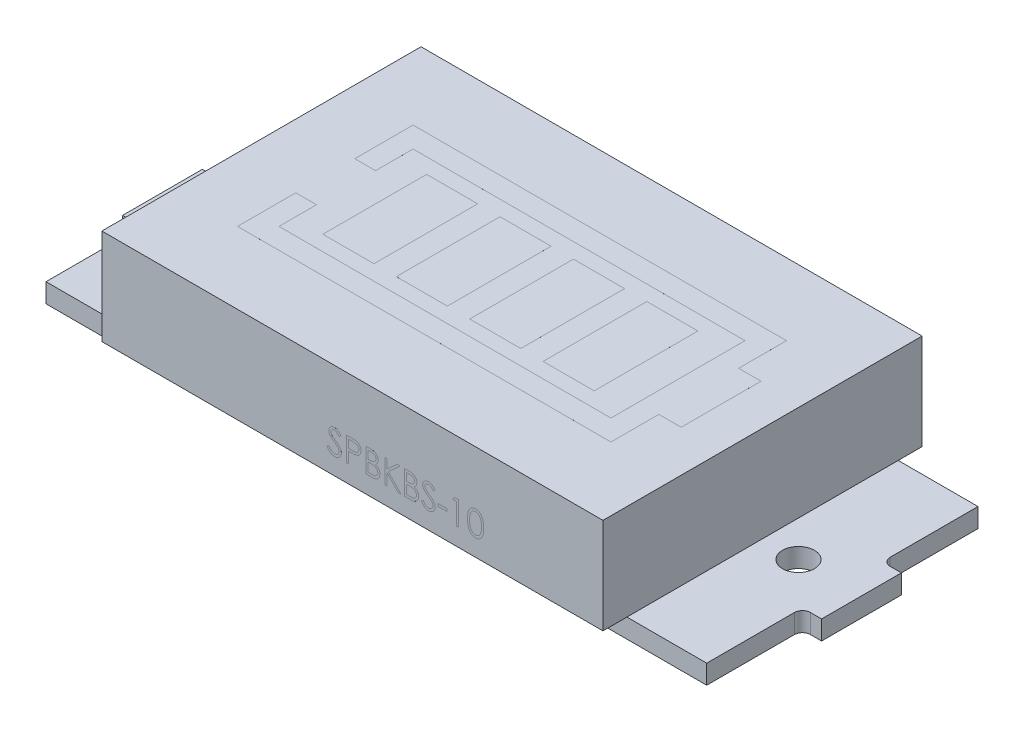
SolidWorks part; units mm, degrees
ref_plane "Plano frontal" through (0, 0, 0) normal (0, 0, 1) x (1, 0, 0)
ref_plane "Plano superior" through (0, 0, 0) normal (0, 1, 0) x (1, 0, 0)
ref_plane "Plano direito" through (0, 0, 0) normal (1, 0, 0) x (0, 0, -1)
sketch "Sketch1" plane through (0, 0, 0) normal (0, 1, 0) x (1, 0, 0)
  line L1 (20.7, -8.5) -> (-20.7, -8.5)
  line L2 (20.7, -8.5) -> (20.7, 8.5)
  line L3 (20.7, 8.5) -> (-20.7, 8.5)
  line L4 (-20.7, -8.5) -> (-20.7, 8.5)
  line L5 (0, 8.5) -> (0, -8.5) construction
  line L6 (20.7, 0) -> (-20.7, 0) construction
  point P0 (0, 0)
  dimension "D1" = 41.4
  dimension "D2" = 17
extrude "Boss-Extrude1" add sketch "Sketch1" along normal mid plane 1.2
sketch "Sketch2" plane through (0, 0, 0) normal (0, 1, 0) x (1, 0, 0)
  line L0 (-20.7, 8.5) -> (-20.7, -8.5) construction
  line L1 (-21.9, 2.5) -> (-20.7, 2.5)
  line L2 (-21.9, 2.5) -> (-21.9, -2.5)
  line L3 (-21.9, -2.5) -> (-20.7, -2.5)
  line L4 (-20.7, 2.5) -> (-20.7, -2.5)
  line L5 (0, -3.9602) -> (0, 3.9602) construction
  line L6 (20.7, 2.5) -> (20.7, -2.5)
  line L7 (21.9, -2.5) -> (20.7, -2.5)
  line L8 (21.9, 2.5) -> (21.9, -2.5)
  line L9 (21.9, 2.5) -> (20.7, 2.5)
  point P6 (-21.9, 0)
  dimension "D1" = 5
  dimension "D2" = 1.2
extrude "Boss-Extrude2" add sketch "Sketch2" along normal mid plane 1.2
fillet "Fillet1" radius 0.5 4 edges at (20.7, 0, -2.5) (20.7, 0, 2.5) (-20.7, 0, 2.5) (-20.7, 0, -2.5)
sketch "Sketch3" plane through (0, 0, 0) normal (0, 1, 0) x (1, 0, 0)
  line L0 (0, -3.9602) -> (0, 3.9602) construction
  circle A0 centre (-17.95, 0) radius 1
  circle A1 centre (17.95, 0) radius 1
  dimension "D1" = 2
  dimension "D2" = 37.9
extrude "Cut-Extrude1" cut sketch "Sketch3" against normal through all both and the other way through all
sketch "Sketch6" plane through (0, -0.6, 0) normal (0, -1, 0) x (1, 0, 0)
  text T0 "<b>MH-DL18S</b>\r\n" font "Century Gothic" height 1
  text T1 "<b>MH-ET-LIVE</b>" font "Century Gothic" height 0.75
extrude "Boss-Extrude5" add sketch "Sketch6" along normal blind 0.0001
sketch "Sketch10" plane through (0, 0, 0) normal (0, 1, 0) x (1, 0, 0)
  line L1 (20.7, 8.5) -> (-20.7, 8.5) construction
  line L3 (-20.7, 8.5) -> (-20.7, 3) construction
  circle A0 centre (-19.2, 7) radius 0.5
  circle A1 centre (-19.2, 4.4) radius 0.5
  dimension "D1" = 1
  dimension "D2" = 1
  dimension "D3" = 1.6
  dimension "D4" = 1
extrude "Cut-Extrude2" cut sketch "Sketch10" against normal through all both and the other way through all
sketch "Sketch11" plane through (0, 0.6, 0) normal (0, 1, 0) x (1, 0, 0)
  line L0 (-19.25, 7) -> (-19.15, 7) construction
  line L1 (-19.25, 7.6) -> (-19.15, 7.6)
  line L2 (-19.25, 6.4) -> (-19.15, 6.4)
  line L3 (-19.25, 4.4) -> (-19.15, 4.4) construction
  line L4 (-19.25, 5) -> (-19.15, 5)
  line L5 (-19.25, 3.8) -> (-19.15, 3.8)
  arc A0 (-19.25, 7.6) -> (-19.25, 6.4) centre (-19.25, 7) ccw
  arc A1 (-19.15, 6.4) -> (-19.15, 7.6) centre (-19.15, 7) ccw
  circle A2 centre (-19.2, 7) radius 0.5 construction
  circle A3 centre (-19.2, 7) radius 0.5
  circle A4 centre (-19.2, 4.4) radius 0.5 construction
  circle A5 centre (-19.2, 4.4) radius 0.5
  arc A6 (-19.25, 5) -> (-19.25, 3.8) centre (-19.25, 4.4) ccw
  arc A7 (-19.15, 3.8) -> (-19.15, 5) centre (-19.15, 4.4) ccw
  point P2 (-19.2, 7)
  point P16 (-19.2, 4.4)
  dimension "D2" = 0.1
  dimension "D1" = 0.05
extrude "Boss-Extrude9" add sketch "Sketch11" along normal blind 0.0001
mirror "Mirror1" about plane through (0, 0, 0) normal (0, 1, 0) of "Boss-Extrude9"
sketch "Sketch12" plane through (0, 0.6, 0) normal (0, 1, 0) x (1, 0, 0)
  line L0 (-20.7, -8.5) -> (20.7, -8.5) construction
  line L1 (-17.6069, 7.1399) -> (-16.6453, 7.1399)
  line L2 (-16.6453, 7.1399) -> (-16.6453, 6.8835)
  line L3 (-16.6453, 6.8835) -> (-17.6069, 6.8835)
  line L4 (-17.6069, 6.8835) -> (-17.6069, 7.1399)
  line L5 (-17.2031, 4.476) -> (-17.2031, 4.9183)
  line L6 (-17.2031, 4.9183) -> (-17.0685, 4.9183)
  line L7 (-17.0685, 4.9183) -> (-17.0685, 4.476)
  line L8 (-17.0685, 4.476) -> (-16.6262, 4.476)
  line L9 (-16.6262, 4.476) -> (-16.6262, 4.3414)
  line L10 (-16.6262, 4.3414) -> (-17.0685, 4.3414)
  line L11 (-17.0685, 4.3414) -> (-17.0685, 3.8991)
  line L12 (-17.0685, 3.8991) -> (-17.2031, 3.8991)
  line L13 (-17.2031, 3.8991) -> (-17.2031, 4.3414)
  line L14 (-17.2031, 4.3414) -> (-17.6454, 4.3414)
  line L15 (-17.6454, 4.3414) -> (-17.6454, 4.476)
  line L16 (-17.6454, 4.476) -> (-17.2031, 4.476)
  line L17 (-17.1261, 7.1399) -> (-17.1261, 6.8835) construction
  line L18 (-17.2031, 4.476) -> (-17.0685, 4.3414) construction
  circle A0 centre (-17.1261, 7.0117) radius 0.5597
  circle A1 centre (-17.1261, 7.0117) radius 0.6597
  circle A2 centre (-17.1358, 4.4087) radius 0.5597
  circle A3 centre (-17.1358, 4.4087) radius 0.6597
  dimension "D2" = 1.1194
  dimension "D1" = 0.1
  dimension "D3" = 0.1
extrude "Boss-Extrude10" add sketch "Sketch12" along normal blind 0.0001 contours A1 A0 | L4 L3 L2 L1 | A3 A2 | L16 L15 L14 L13 L12 L11 L10 L9 L8 L7 L6 L5
sketch "Sketch4" plane through (0, 0.6, 0) normal (0, 1, 0) x (1, 0, 0)
  line L1 (15.7, -10) -> (-15.7, -10)
  line L2 (15.7, -10) -> (15.7, 10)
  line L3 (15.7, 10) -> (-15.7, 10)
  line L4 (-15.7, -10) -> (-15.7, 10)
  line L5 (0, 10) -> (0, -10) construction
  line L6 (15.7, 0) -> (-15.7, 0) construction
  point P0 (0, 0)
  dimension "D1" = 31.4
  dimension "D2" = 20
extrude "Boss-Extrude3" add sketch "Sketch4" along normal blind 6
sketch "Sketch5" plane through (0, 6.6, 0) normal (0, 1, 0) x (1, 0, 0)
  line L4 (-15.7, 10) -> (-15.7, -10)
  line L5 (-15.7, -10) -> (15.7, -10)
  line L6 (15.7, -10) -> (15.7, 10)
  line L7 (15.7, 10) -> (-15.7, 10)
  line L8 (-15.7, 10) -> (-15.7, -10)
  line L9 (-15.7, -10) -> (15.7, -10)
  line L10 (15.7, -10) -> (15.7, 10)
  line L11 (15.7, 10) -> (-15.7, 10)
  dimension "D1" = 0
extrude "Boss-Extrude4" add sketch "Sketch5" along normal blind 0.0001
sketch "Sketch7" plane through (0, 6.6001, 0) normal (0, 1, 0) x (1, 0, 0)
  line L0 (10.4, -4.2) -> (-10.4, -4.2)
  line L1 (11.7, -5.5) -> (-11.7, -5.5)
  line L2 (11.7, -5.5) -> (11.7, -2.5)
  line L3 (11.7, 5.5) -> (-11.7, 5.5)
  line L4 (-11.7, -5.5) -> (-11.7, -1.85)
  line L5 (0, 5.5) -> (0, -5.5) construction
  line L6 (10.4, 0) -> (-10.4, 0) construction
  line L7 (-10.4, -4.2) -> (-10.4, 4.2)
  line L8 (10.4, 4.2) -> (-10.4, 4.2)
  line L9 (10.4, -4.2) -> (10.4, 4.2)
  line L10 (-11.7, 1.85) -> (-10.4, 1.85)
  line L11 (-11.7, -1.85) -> (-10.4, -1.85)
  line L12 (-11.7, 1.85) -> (-11.7, 5.5)
  line L13 (11.7, 2.5) -> (11.7, 5.5)
  line L14 (-11.7, -5.5) -> (-11.7, 5.5) construction
  line L15 (11.7, 2.5) -> (13.1, 2.5)
  line L17 (11.7, -2.5) -> (13.1, -2.5)
  line L18 (13.1, 2.5) -> (13.1, -2.5)
  line L20 (11.7, -5.5) -> (11.7, 5.5) construction
  point P0 (0, 0)
  point P17 (13.1, 0)
  dimension "D1" = 23.4
  dimension "D2" = 11
  dimension "D4" = 3.7
  dimension "D5" = 5
  dimension "D6" = 1.4
  dimension "D7" = 3.65
  dimension "D3" = 1.3
extrude "Boss-Extrude6" add sketch "Sketch7" along normal blind 0.0001 contours L18 L15 L13 L3 L12 L10 L7 L8 L9 L0 L11 L4 L1 L2 L17
sketch "Sketch8" plane through (0, 6.6001, 0) normal (0, 1, 0) x (1, 0, 0)
  line L0 (-10.4, 1.85) -> (-10.4, 4.2) construction
  line L1 (-8.6, 3.25) -> (-5.4, 3.25)
  line L2 (-8.6, 3.25) -> (-8.6, -3.25)
  line L3 (-8.6, -3.25) -> (-5.4, -3.25)
  line L4 (-5.4, 3.25) -> (-5.4, -3.25)
  line L5 (-4, 3.25) -> (-0.8, 3.25)
  line L6 (-4, 3.25) -> (-4, -3.25)
  line L7 (-4, -3.25) -> (-0.8, -3.25)
  line L8 (-0.8, 3.25) -> (-0.8, -3.25)
  line L9 (0.6, 3.25) -> (3.8, 3.25)
  line L10 (0.6, 3.25) -> (0.6, -3.25)
  line L11 (0.6, -3.25) -> (3.8, -3.25)
  line L12 (3.8, 3.25) -> (3.8, -3.25)
  line L13 (5.2, 3.25) -> (8.4, 3.25)
  line L14 (5.2, 3.25) -> (5.2, -3.25)
  line L15 (5.2, -3.25) -> (8.4, -3.25)
  line L16 (8.4, 3.25) -> (8.4, -3.25)
  line L17 (10.4, -4.2) -> (10.4, 4.2) construction
  point P4 (-5.4, 0)
  dimension "D1" = 3.2
  dimension "D2" = 6.5
  dimension "D3" = 1.8
  dimension "D5" = 2
  dimension "D4" = 4
extrude "Boss-Extrude7" add sketch "Sketch8" along normal blind 0.0001
sketch "Sketch9" plane through (0, 0, 10) normal (0, 0, 1) x (1, 0, 0)
  text T0 "SPBKBS-10" font "Century Gothic" height 1.5
extrude "Boss-Extrude8" add sketch "Sketch9" along normal blind 0.0001
